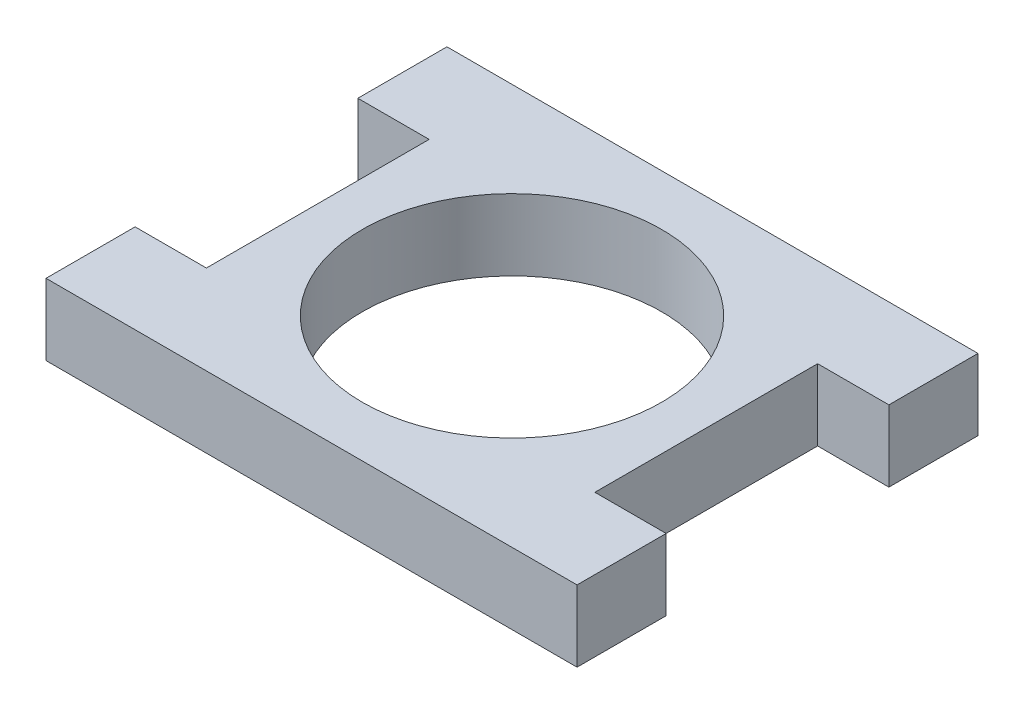
SolidWorks part; units mm, degrees
ref_plane "Front Plane" through (0, 0, 0) normal (0, 0, 1) x (1, 0, 0)
ref_plane "Top Plane" through (0, 0, 0) normal (0, 1, 0) x (1, 0, 0)
ref_plane "Right Plane" through (0, 0, 0) normal (1, 0, 0) x (0, 0, -1)
sketch "Sketch1" plane through (0, 0, 0) normal (0, 1, 0) x (1, 0, 0)
  line L1 (-13.843, 14.2875) -> (13.843, 14.2875)
  line L2 (-13.843, 14.2875) -> (-13.843, -14.2875)
  line L3 (-13.843, -14.2875) -> (13.843, -14.2875)
  line L4 (13.843, 14.2875) -> (13.843, -14.2875)
  line L5 (-13.843, 14.2875) -> (13.843, -14.2875) construction
  line L6 (-13.843, -14.2875) -> (13.843, 14.2875) construction
  line L7 (-13.843, 14.2875) -> (-18.923, 14.2875)
  line L8 (-13.843, 14.2875) -> (-13.843, 7.9375)
  line L9 (-13.843, 7.9375) -> (-18.923, 7.9375)
  line L10 (-18.923, 14.2875) -> (-18.923, 7.9375)
  line L11 (-13.843, -14.2875) -> (-18.923, -14.2875)
  line L12 (-13.843, -14.2875) -> (-13.843, -7.9375)
  line L13 (-13.843, -7.9375) -> (-18.923, -7.9375)
  line L14 (-18.923, -14.2875) -> (-18.923, -7.9375)
  line L15 (13.843, -14.2875) -> (18.923, -14.2875)
  line L16 (13.843, -14.2875) -> (13.843, -7.9375)
  line L17 (13.843, -7.9375) -> (18.923, -7.9375)
  line L18 (18.923, -14.2875) -> (18.923, -7.9375)
  line L19 (13.843, 14.2875) -> (18.923, 14.2875)
  line L20 (13.843, 14.2875) -> (13.843, 7.9375)
  line L21 (13.843, 7.9375) -> (18.923, 7.9375)
  line L22 (18.923, 14.2875) -> (18.923, 7.9375)
  circle A0 centre (0, 0) radius 10.668
  dimension "D1" = 21.336
  dimension "D2" = 27.686
  dimension "D3" = 28.575
  dimension "D4" = 5.08
  dimension "D5" = 6.35
extrude "Boss-Extrude1" add sketch "Sketch1" along normal blind 5.08 contours L14 L11 L2 L13 | L7 L10 L9 L2 | L4 L1 L2 L3 A0 | L22 L19 L4 L21 | L15 L18 L17 L4
